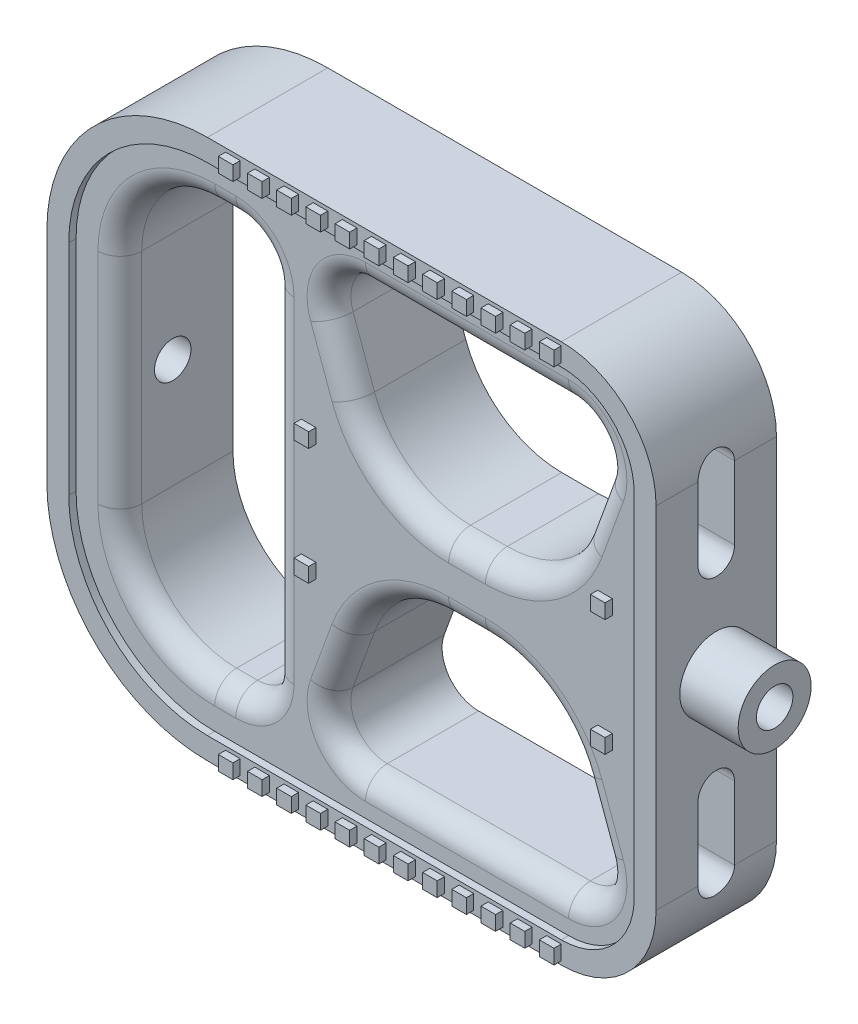
SolidWorks part; units mm, degrees
ref_plane "Front Plane" through (0, 0, 0) normal (0, 0, 1) x (1, 0, 0)
ref_plane "Top Plane" through (0, 0, 0) normal (0, 1, 0) x (1, 0, 0)
ref_plane "Right Plane" through (0, 0, 0) normal (1, 0, 0) x (0, 0, -1)
sketch "Sketch1" plane through (0, 0, 0) normal (0, 0, 1) x (1, 0, 0)
  line L1 (-41.75, 37) -> (41.75, 37)
  line L2 (-41.75, 37) -> (-41.75, -37)
  line L3 (-41.75, -37) -> (41.75, -37)
  line L4 (41.75, 37) -> (41.75, -37)
  line L5 (-41.75, 37) -> (41.75, -37) construction
  line L6 (-41.75, -37) -> (41.75, 37) construction
  point P0 (0, 0)
  dimension "D1" = 74
  dimension "D2" = 83.5
extrude "Boss-Extrude1" add sketch "Sketch1" along normal blind 16.5
fillet "Fillet1" radius 13 2 edges at (41.75, -37, 8.25) (41.75, 37, 8.25)
fillet "Fillet2" radius 22 2 edges at (-41.75, -37, 8.25) (-41.75, 37, 8.25)
sketch "Sketch2" plane through (0, 0, 16.5) normal (0, 0, 1) x (1, 0, 0)
  line L0 (-38.75, 15) -> (-38.75, -15)
  line L1 (-19.75, -34) -> (28.75, -34)
  line L2 (38.75, -24) -> (38.75, 24)
  line L3 (28.75, 34) -> (-19.75, 34)
  line L4 (-41.75, 15) -> (-41.75, -15)
  line L5 (-19.75, -37) -> (28.75, -37)
  line L6 (41.75, -24) -> (41.75, 24)
  line L7 (28.75, 37) -> (-19.75, 37)
  line L8 (-41.75, 15) -> (-41.75, -15)
  line L9 (-19.75, -37) -> (28.75, -37)
  line L10 (41.75, -24) -> (41.75, 24)
  line L11 (28.75, 37) -> (-19.75, 37)
  arc A0 (-19.75, 34) -> (-38.75, 15) centre (-19.75, 15) ccw
  arc A1 (-38.75, -15) -> (-19.75, -34) centre (-19.75, -15) ccw
  arc A2 (28.75, -34) -> (38.75, -24) centre (28.75, -24) ccw
  arc A3 (38.75, 24) -> (28.75, 34) centre (28.75, 24) ccw
  arc A4 (-41.75, -15) -> (-19.75, -37) centre (-19.75, -15) ccw
  arc A5 (28.75, -37) -> (41.75, -24) centre (28.75, -24) ccw
  arc A6 (41.75, 24) -> (28.75, 37) centre (28.75, 24) ccw
  arc A7 (-19.75, 37) -> (-41.75, 15) centre (-19.75, 15) ccw
  arc A8 (-41.75, -15) -> (-19.75, -37) centre (-19.75, -15) ccw
  arc A9 (28.75, -37) -> (41.75, -24) centre (28.75, -24) ccw
  arc A10 (41.75, 24) -> (28.75, 37) centre (28.75, 24) ccw
  arc A11 (-19.75, 37) -> (-41.75, 15) centre (-19.75, 15) ccw
  dimension "D1" = 0
  dimension "D2" = 3
extrude "Cut-Extrude1" cut sketch "Sketch2" against normal blind 1 contours A0 L0 A1 L1 A2 L2 A3 L3
sketch "Sketch4" plane through (41.75, 0, 0) normal (1, 0, 0) x (0, 0, -1)
  line L0 (-16.5, 0) -> (0, 0) construction
  line L3 (-16.5, -24) -> (-16.5, 24) construction
  line L6 (-8.25, 24) -> (-8.25, -24) construction
  line L7 (0, 24) -> (-16.5, 24) construction
  line L8 (-16.5, -24) -> (0, -24) construction
  circle A4 centre (-8.25, 0) radius 5
  dimension "D1" = 10
extrude "Boss-Extrude2" add sketch "Sketch4" along normal blind 8
sketch "Sketch5" plane through (41.75, 0, 0) normal (1, 0, 0) x (0, 0, -1)
  line L0 (-8.25, 24) -> (-8.25, 14) construction
  line L1 (-5.75, 24) -> (-5.75, 14)
  line L2 (-10.75, 24) -> (-10.75, 14)
  line L3 (-16.5, 0) -> (0, 0) construction
  line L4 (-16.5, -24) -> (-16.5, 24) construction
  line L5 (-8.25, -24) -> (-8.25, -14) construction
  line L6 (-5.75, -24) -> (-5.75, -14)
  line L7 (-10.75, -24) -> (-10.75, -14)
  line L8 (-16.5, -24) -> (-16.5, -37) construction
  line L9 (-16.5, -37) -> (0, -37) construction
  line L10 (0, -37) -> (0, -24) construction
  line L11 (0, -24) -> (-16.5, -24) construction
  line L12 (-16.5, 37) -> (-16.5, 24) construction
  line L13 (-16.5, 24) -> (0, 24) construction
  line L14 (0, 24) -> (0, 37) construction
  line L15 (0, 37) -> (-16.5, 37) construction
  line L16 (-16.5, -24) -> (-16.5, -37)
  line L17 (-16.5, -37) -> (0, -37)
  line L18 (0, -37) -> (0, -24)
  line L19 (0, -24) -> (-16.5, -24)
  line L20 (-16.5, 37) -> (-16.5, 24)
  line L21 (-16.5, 24) -> (0, 24)
  line L22 (0, 24) -> (0, 37)
  line L23 (0, 37) -> (-16.5, 37)
  circle A0 centre (-8.25, 0) radius 5 construction
  circle A1 centre (-8.25, 0) radius 5
  arc A2 (-5.75, 24) -> (-10.75, 24) centre (-8.25, 24) ccw
  arc A3 (-10.75, 14) -> (-5.75, 14) centre (-8.25, 14) ccw
  arc A4 (-5.75, -24) -> (-10.75, -24) centre (-8.25, -24) cw
  arc A5 (-10.75, -14) -> (-5.75, -14) centre (-8.25, -14) cw
  point P5 (-8.25, 19)
  point P17 (-8.25, -19)
  line M9 (-16.5, -24) -> (0, -24)
  line M11 (0, 24) -> (-16.5, 24)
  dimension "D1" = 10
  dimension "D2" = 5
  dimension "D3" = 14
sketch "Sketch6" plane through (0, 0, 15.5) normal (0, 0, 1) x (1, 0, 0)
  line L0 (-38.75, 0) -> (38.75, 0) construction
  line L1 (-19.75, 28) -> (-16.875, 28)
  line L2 (-32.75, 15) -> (-32.75, -15)
  line L3 (-19.75, -28) -> (-16.875, -28)
  line L4 (28.75, 34) -> (-19.75, 34)
  line L5 (-38.75, 15) -> (-38.75, -15)
  line L6 (-19.75, -34) -> (28.75, -34)
  line L7 (38.75, -24) -> (38.75, 24)
  line L8 (28.75, 34) -> (-19.75, 34)
  line L9 (-38.75, 15) -> (-38.75, -15)
  line L10 (-19.75, -34) -> (28.75, -34)
  line L11 (38.75, -24) -> (38.75, 24)
  line L12 (-11.875, 23) -> (-11.875, -23)
  line L13 (0.9167, 29) -> (28.75, 29)
  line L18 (33.4485, 22.2899) -> (30.5082, 14.2117)
  line L19 (17.3525, 5) -> (12.3141, 5)
  line L20 (-0.8416, 14.2117) -> (-3.7818, 22.2899)
  line L21 (17.3525, -5) -> (12.3141, -5)
  line L22 (33.4485, -22.2899) -> (30.5082, -14.2117)
  line L23 (0.9167, -29) -> (28.75, -29)
  line L24 (-0.8416, -14.2117) -> (-3.7818, -22.2899)
  arc A0 (-32.75, -15) -> (-19.75, -28) centre (-19.75, -15) ccw
  arc A1 (-19.75, 28) -> (-32.75, 15) centre (-19.75, 15) ccw
  arc A2 (-16.875, -28) -> (-11.875, -23) centre (-16.875, -23) ccw
  arc A3 (-16.875, 28) -> (-11.875, 23) centre (-16.875, 23) cw
  arc A4 (-19.75, 34) -> (-38.75, 15) centre (-19.75, 15) ccw
  arc A5 (-38.75, -15) -> (-19.75, -34) centre (-19.75, -15) ccw
  arc A6 (28.75, -34) -> (38.75, -24) centre (28.75, -24) ccw
  arc A7 (38.75, 24) -> (28.75, 34) centre (28.75, 24) ccw
  arc A8 (-19.75, 34) -> (-38.75, 15) centre (-19.75, 15) ccw
  arc A9 (-38.75, -15) -> (-19.75, -34) centre (-19.75, -15) ccw
  arc A10 (28.75, -34) -> (38.75, -24) centre (28.75, -24) ccw
  arc A11 (38.75, 24) -> (28.75, 34) centre (28.75, 24) ccw
  arc A12 (28.75, 29) -> (33.4485, 22.2899) centre (28.75, 24) cw
  arc A13 (0.9167, 29) -> (-3.7818, 22.2899) centre (0.9167, 24) ccw
  arc A14 (28.75, -29) -> (33.4485, -22.2899) centre (28.75, -24) ccw
  arc A15 (0.9167, -29) -> (-3.7818, -22.2899) centre (0.9167, -24) cw
  arc A16 (30.5082, 14.2117) -> (17.3525, 5) centre (17.3525, 19) cw
  arc A17 (12.3141, 5) -> (-0.8416, 14.2117) centre (12.3141, 19) cw
  arc A18 (17.3525, -5) -> (30.5082, -14.2117) centre (17.3525, -19) cw
  arc A19 (12.3141, -5) -> (-0.8416, -14.2117) centre (12.3141, -19) ccw
  point P18 (-32.75, -28)
  point P23 (-11.875, -28)
  point P46 (27.1555, 5)
  point P49 (2.5112, 5)
  point P52 (27.1555, -5)
  point P55 (2.5112, -5)
  dimension "D4" = 5
  dimension "D3" = 13
  dimension "D6" = 5
  dimension "D9" = 14
  dimension "D10" = 14
  dimension "D2" = 20.875
  dimension "D5" = 70
  dimension "D7" = 27.8333
  dimension "D8" = 10
  dimension "D1" = 0
extrude "Cut-Extrude2" cut sketch "Sketch6" against normal through all contours A1 L1 A3 L12 A2 L3 A0 L2 | L20 A13 L13 A12 L18 A16 L19 A17 | L21 A19 L24 A15 L23 A14 L22 A18
extrude "Cut-Extrude7" cut sketch "Sketch5" against normal up to next contours L2 A3 L1 M11 | L1 A2 L2 M11 | A5 L7 L6 M9 | A4 L6 L7 M9
sketch "Sketch7" plane through (49.75, 0, 0) normal (1, 0, 0) x (0, 0, -1)
  circle A0 centre (-8.25, 0) radius 2.5
  circle A1 centre (-8.25, 0) radius 5
  circle A2 centre (-8.25, 0) radius 5
  dimension "D2" = 5
  dimension "D1" = 0
extrude "Cut-Extrude9" cut sketch "Sketch7" against normal through all contours A0
fillet "Fillet3" radius 3 24 edges at (25.3826, -7.5319, 15.5) (31.9784, -18.2508, 15.5) (32.8458, -26.8679, 15.5) (14.8333, -29, 15.5) (-3.1791, -26.8679, 15.5) (-2.3117, -18.2508, 15.5) (4.284, -7.5319, 15.5) (25.3826, 7.5319, 15.5) (31.9784, 18.2508, 15.5) (32.8458, 26.8679, 15.5) (14.8333, 29, 15.5) (-3.1791, 26.8679, 15.5) (-2.3117, 18.2508, 15.5) (4.284, 7.5319, 15.5) (-28.9424, 24.1924, 15.5) (-18.3125, 28, 15.5) (-13.3395, 26.5355, 15.5) (-11.875, 0, 15.5) (-13.3395, -26.5355, 15.5) (-18.3125, -28, 15.5) (-28.9424, -24.1924, 15.5) (14.8333, -5, 15.5) (14.8333, 5, 15.5) (-32.75, 0, 15.5)
fillet "Fillet4" [suppressed] radius 1
sketch "Sketch8" plane through (0, 0, 15.5) normal (0, 0, 1) x (1, 0, 0)
  line L0 (-11.875, -23) -> (-11.875, 23) construction
  line L1 (-7.875, -7) -> (-5.875, -7)
  line L2 (-7.875, -7) -> (-7.875, -9)
  line L3 (-7.875, -9) -> (-5.875, -9)
  line L4 (-5.875, -7) -> (-5.875, -9)
  line L5 (32.75, -7) -> (34.75, -7)
  line L6 (32.75, -7) -> (32.75, -9)
  line L7 (32.75, -9) -> (34.75, -9)
  line L8 (34.75, -7) -> (34.75, -9)
  line L9 (41.75, -24) -> (41.75, 24) construction
  line L10 (-41.75, 0) -> (49.75, 0) construction
  line L11 (-41.75, 15) -> (-41.75, -15) construction
  line L12 (49.75, -5) -> (49.75, 5) construction
  line L13 (32.75, 9) -> (34.75, 9)
  line L14 (34.75, 7) -> (34.75, 9)
  line L15 (32.75, 7) -> (34.75, 7)
  line L16 (32.75, 7) -> (32.75, 9)
  line L17 (-7.875, 9) -> (-5.875, 9)
  line L18 (-5.875, 7) -> (-5.875, 9)
  line L19 (-7.875, 7) -> (-5.875, 7)
  line L20 (-7.875, 7) -> (-7.875, 9)
  line L22 (26.75, 36.5) -> (28.75, 36.5)
  line L23 (26.75, 36.5) -> (26.75, 34.5)
  line L24 (26.75, 34.5) -> (28.75, 34.5)
  line L25 (28.75, 36.5) -> (28.75, 34.5)
  line L26 (28.75, 37) -> (-19.75, 37) construction
  line L27 (22.75, 36.5) -> (22.75, 34.5)
  line L28 (22.75, 36.5) -> (24.75, 36.5)
  line L29 (24.75, 36.5) -> (24.75, 34.5)
  line L30 (22.75, 34.5) -> (24.75, 34.5)
  line L31 (18.75, 36.5) -> (18.75, 34.5)
  line L32 (18.75, 36.5) -> (20.75, 36.5)
  line L33 (20.75, 36.5) -> (20.75, 34.5)
  line L34 (18.75, 34.5) -> (20.75, 34.5)
  line L35 (14.75, 36.5) -> (14.75, 34.5)
  line L36 (14.75, 36.5) -> (16.75, 36.5)
  line L37 (16.75, 36.5) -> (16.75, 34.5)
  line L38 (14.75, 34.5) -> (16.75, 34.5)
  line L39 (10.75, 36.5) -> (10.75, 34.5)
  line L40 (10.75, 36.5) -> (12.75, 36.5)
  line L41 (12.75, 36.5) -> (12.75, 34.5)
  line L42 (10.75, 34.5) -> (12.75, 34.5)
  line L43 (6.75, 36.5) -> (6.75, 34.5)
  line L44 (6.75, 36.5) -> (8.75, 36.5)
  line L45 (8.75, 36.5) -> (8.75, 34.5)
  line L46 (6.75, 34.5) -> (8.75, 34.5)
  line L47 (2.75, 36.5) -> (2.75, 34.5)
  line L48 (2.75, 36.5) -> (4.75, 36.5)
  line L49 (4.75, 36.5) -> (4.75, 34.5)
  line L50 (2.75, 34.5) -> (4.75, 34.5)
  line L51 (-1.25, 36.5) -> (-1.25, 34.5)
  line L52 (-1.25, 36.5) -> (0.75, 36.5)
  line L53 (0.75, 36.5) -> (0.75, 34.5)
  line L54 (-1.25, 34.5) -> (0.75, 34.5)
  line L55 (-5.25, 36.5) -> (-5.25, 34.5)
  line L56 (-5.25, 36.5) -> (-3.25, 36.5)
  line L57 (-3.25, 36.5) -> (-3.25, 34.5)
  line L58 (-5.25, 34.5) -> (-3.25, 34.5)
  line L59 (-9.25, 36.5) -> (-9.25, 34.5)
  line L60 (-9.25, 36.5) -> (-7.25, 36.5)
  line L61 (-7.25, 36.5) -> (-7.25, 34.5)
  line L62 (-9.25, 34.5) -> (-7.25, 34.5)
  line L63 (-13.25, 36.5) -> (-13.25, 34.5)
  line L64 (-13.25, 36.5) -> (-11.25, 36.5)
  line L65 (-11.25, 36.5) -> (-11.25, 34.5)
  line L66 (-13.25, 34.5) -> (-11.25, 34.5)
  line L67 (-17.25, 36.5) -> (-17.25, 34.5)
  line L68 (-17.25, 36.5) -> (-15.25, 36.5)
  line L69 (-15.25, 36.5) -> (-15.25, 34.5)
  line L70 (-17.25, 34.5) -> (-15.25, 34.5)
  line L71 (28.75, -36.5) -> (28.75, -34.5)
  line L72 (26.75, -36.5) -> (28.75, -36.5)
  line L73 (26.75, -36.5) -> (26.75, -34.5)
  line L74 (26.75, -34.5) -> (28.75, -34.5)
  line L75 (24.75, -36.5) -> (24.75, -34.5)
  line L76 (22.75, -34.5) -> (24.75, -34.5)
  line L77 (22.75, -36.5) -> (22.75, -34.5)
  line L78 (22.75, -36.5) -> (24.75, -36.5)
  line L79 (20.75, -36.5) -> (20.75, -34.5)
  line L80 (18.75, -34.5) -> (20.75, -34.5)
  line L81 (18.75, -36.5) -> (18.75, -34.5)
  line L82 (18.75, -36.5) -> (20.75, -36.5)
  line L83 (16.75, -36.5) -> (16.75, -34.5)
  line L84 (14.75, -34.5) -> (16.75, -34.5)
  line L85 (14.75, -36.5) -> (14.75, -34.5)
  line L86 (14.75, -36.5) -> (16.75, -36.5)
  line L87 (12.75, -36.5) -> (12.75, -34.5)
  line L88 (10.75, -34.5) -> (12.75, -34.5)
  line L89 (10.75, -36.5) -> (10.75, -34.5)
  line L90 (10.75, -36.5) -> (12.75, -36.5)
  line L91 (8.75, -36.5) -> (8.75, -34.5)
  line L92 (6.75, -34.5) -> (8.75, -34.5)
  line L93 (6.75, -36.5) -> (6.75, -34.5)
  line L94 (6.75, -36.5) -> (8.75, -36.5)
  line L95 (4.75, -36.5) -> (4.75, -34.5)
  line L96 (2.75, -34.5) -> (4.75, -34.5)
  line L97 (2.75, -36.5) -> (2.75, -34.5)
  line L98 (2.75, -36.5) -> (4.75, -36.5)
  line L99 (0.75, -36.5) -> (0.75, -34.5)
  line L100 (-1.25, -34.5) -> (0.75, -34.5)
  line L101 (-1.25, -36.5) -> (-1.25, -34.5)
  line L102 (-1.25, -36.5) -> (0.75, -36.5)
  line L103 (-3.25, -36.5) -> (-3.25, -34.5)
  line L104 (-5.25, -34.5) -> (-3.25, -34.5)
  line L105 (-5.25, -36.5) -> (-5.25, -34.5)
  line L106 (-5.25, -36.5) -> (-3.25, -36.5)
  line L107 (-7.25, -36.5) -> (-7.25, -34.5)
  line L108 (-9.25, -34.5) -> (-7.25, -34.5)
  line L109 (-9.25, -36.5) -> (-9.25, -34.5)
  line L110 (-9.25, -36.5) -> (-7.25, -36.5)
  line L111 (-11.25, -36.5) -> (-11.25, -34.5)
  line L112 (-13.25, -34.5) -> (-11.25, -34.5)
  line L113 (-13.25, -36.5) -> (-13.25, -34.5)
  line L114 (-13.25, -36.5) -> (-11.25, -36.5)
  line L115 (-15.25, -36.5) -> (-15.25, -34.5)
  line L116 (-17.25, -34.5) -> (-15.25, -34.5)
  line L117 (-17.25, -36.5) -> (-17.25, -34.5)
  line L118 (-17.25, -36.5) -> (-15.25, -36.5)
  dimension "D1" = 2
  dimension "D2" = 2
  dimension "D3" = 4
  dimension "D4" = 2
  dimension "D5" = 2
  dimension "D6" = 7
  dimension "D7" = 14
  dimension "D8" = 14
  dimension "D9" = 2
  dimension "D10" = 2
  dimension "D11" = 0.5
  dimension "D12" = 13
  dimension "D14" = 4
  dimension "D16" = 4
  dimension "D13" = 12
  dimension "D15" = 12
extrude "Boss-Extrude4" add sketch "Sketch8" along normal blind 1
sketch "Sketch9" plane through (0, 0, 16.5) normal (0, 0, 1) x (1, 0, 0)
  line L0 (28.75, 37) -> (-19.75, 37) construction
  line L1 (26.75, 36.5) -> (28.75, 36.5)
  line L2 (26.75, 36.5) -> (26.75, 34.5)
  line L3 (26.75, 34.5) -> (28.75, 34.5)
  line L4 (28.75, 36.5) -> (28.75, 34.5)
  line L5 (41.75, -24) -> (41.75, 24) construction
  line L6 (-41.75, 0) -> (49.75, 0) construction
  line L7 (-41.75, 15) -> (-41.75, -15) construction
  line L8 (49.75, -5) -> (49.75, 5) construction
  line L9 (26.75, -34.5) -> (28.75, -34.5)
  line L10 (28.75, -36.5) -> (28.75, -34.5)
  line L11 (26.75, -36.5) -> (28.75, -36.5)
  line L12 (26.75, -36.5) -> (26.75, -34.5)
  line L13 (22.75, 36.5) -> (22.75, 34.5)
  line L14 (22.75, 36.5) -> (24.75, 36.5)
  line L15 (24.75, 36.5) -> (24.75, 34.5)
  line L16 (22.75, 34.5) -> (24.75, 34.5)
  line L17 (22.75, -34.5) -> (24.75, -34.5)
  line L18 (24.75, -36.5) -> (24.75, -34.5)
  line L19 (22.75, -36.5) -> (24.75, -36.5)
  line L20 (22.75, -36.5) -> (22.75, -34.5)
  line L21 (18.75, 36.5) -> (18.75, 34.5)
  line L22 (18.75, 36.5) -> (20.75, 36.5)
  line L23 (20.75, 36.5) -> (20.75, 34.5)
  line L24 (18.75, 34.5) -> (20.75, 34.5)
  line L25 (18.75, -34.5) -> (20.75, -34.5)
  line L26 (20.75, -36.5) -> (20.75, -34.5)
  line L27 (18.75, -36.5) -> (20.75, -36.5)
  line L28 (18.75, -36.5) -> (18.75, -34.5)
  line L29 (14.75, 36.5) -> (14.75, 34.5)
  line L30 (14.75, 36.5) -> (16.75, 36.5)
  line L31 (16.75, 36.5) -> (16.75, 34.5)
  line L32 (14.75, 34.5) -> (16.75, 34.5)
  line L33 (14.75, -34.5) -> (16.75, -34.5)
  line L34 (16.75, -36.5) -> (16.75, -34.5)
  line L35 (14.75, -36.5) -> (16.75, -36.5)
  line L36 (14.75, -36.5) -> (14.75, -34.5)
  line L37 (10.75, 36.5) -> (10.75, 34.5)
  line L38 (10.75, 36.5) -> (12.75, 36.5)
  line L39 (12.75, 36.5) -> (12.75, 34.5)
  line L40 (10.75, 34.5) -> (12.75, 34.5)
  line L41 (10.75, -34.5) -> (12.75, -34.5)
  line L42 (12.75, -36.5) -> (12.75, -34.5)
  line L43 (10.75, -36.5) -> (12.75, -36.5)
  line L44 (10.75, -36.5) -> (10.75, -34.5)
  line L45 (6.75, 36.5) -> (6.75, 34.5)
  line L46 (6.75, 36.5) -> (8.75, 36.5)
  line L47 (8.75, 36.5) -> (8.75, 34.5)
  line L48 (6.75, 34.5) -> (8.75, 34.5)
  line L49 (6.75, -34.5) -> (8.75, -34.5)
  line L50 (8.75, -36.5) -> (8.75, -34.5)
  line L51 (6.75, -36.5) -> (8.75, -36.5)
  line L52 (6.75, -36.5) -> (6.75, -34.5)
  line L53 (2.75, 36.5) -> (2.75, 34.5)
  line L54 (2.75, 36.5) -> (4.75, 36.5)
  line L55 (4.75, 36.5) -> (4.75, 34.5)
  line L56 (2.75, 34.5) -> (4.75, 34.5)
  line L57 (2.75, -34.5) -> (4.75, -34.5)
  line L58 (4.75, -36.5) -> (4.75, -34.5)
  line L59 (2.75, -36.5) -> (4.75, -36.5)
  line L60 (2.75, -36.5) -> (2.75, -34.5)
  line L61 (-1.25, 36.5) -> (-1.25, 34.5)
  line L62 (-1.25, 36.5) -> (0.75, 36.5)
  line L63 (0.75, 36.5) -> (0.75, 34.5)
  line L64 (-1.25, 34.5) -> (0.75, 34.5)
  line L65 (-1.25, -34.5) -> (0.75, -34.5)
  line L66 (0.75, -36.5) -> (0.75, -34.5)
  line L67 (-1.25, -36.5) -> (0.75, -36.5)
  line L68 (-1.25, -36.5) -> (-1.25, -34.5)
  line L69 (-5.25, 36.5) -> (-5.25, 34.5)
  line L70 (-5.25, 36.5) -> (-3.25, 36.5)
  line L71 (-3.25, 36.5) -> (-3.25, 34.5)
  line L72 (-5.25, 34.5) -> (-3.25, 34.5)
  line L73 (-5.25, -34.5) -> (-3.25, -34.5)
  line L74 (-3.25, -36.5) -> (-3.25, -34.5)
  line L75 (-5.25, -36.5) -> (-3.25, -36.5)
  line L76 (-5.25, -36.5) -> (-5.25, -34.5)
  line L77 (-9.25, 36.5) -> (-9.25, 34.5)
  line L78 (-9.25, 36.5) -> (-7.25, 36.5)
  line L79 (-7.25, 36.5) -> (-7.25, 34.5)
  line L80 (-9.25, 34.5) -> (-7.25, 34.5)
  line L81 (-9.25, -34.5) -> (-7.25, -34.5)
  line L82 (-7.25, -36.5) -> (-7.25, -34.5)
  line L83 (-9.25, -36.5) -> (-7.25, -36.5)
  line L84 (-9.25, -36.5) -> (-9.25, -34.5)
  line L85 (-13.25, 36.5) -> (-13.25, 34.5)
  line L86 (-13.25, 36.5) -> (-11.25, 36.5)
  line L87 (-11.25, 36.5) -> (-11.25, 34.5)
  line L88 (-13.25, 34.5) -> (-11.25, 34.5)
  line L89 (-13.25, -34.5) -> (-11.25, -34.5)
  line L90 (-11.25, -36.5) -> (-11.25, -34.5)
  line L91 (-13.25, -36.5) -> (-11.25, -36.5)
  line L92 (-13.25, -36.5) -> (-13.25, -34.5)
  line L93 (-17.25, 36.5) -> (-17.25, 34.5)
  line L94 (-17.25, 36.5) -> (-15.25, 36.5)
  line L95 (-15.25, 36.5) -> (-15.25, 34.5)
  line L96 (-17.25, 34.5) -> (-15.25, 34.5)
  line L97 (-17.25, -34.5) -> (-15.25, -34.5)
  line L98 (-15.25, -36.5) -> (-15.25, -34.5)
  line L99 (-17.25, -36.5) -> (-15.25, -36.5)
  line L100 (-17.25, -36.5) -> (-17.25, -34.5)
  dimension "D1" = 2
  dimension "D2" = 2
  dimension "D3" = 0.5
  dimension "D4" = 13
  dimension "D6" = 4
  dimension "D5" = 12
extrude "Boss-Extrude5" add sketch "Sketch9" along normal blind 1
equation "\"A\"= 74"
equation "\"B\"= 83.5"
equation "\"C\"= 16.5"
equation "\"D1@Sketch1\"= \"A\""
equation "\"D2@Sketch1\"= \"B\""
equation "\"D1@Boss-Extrude1\"=\"C\""
equation "\"D2@Sketch6\"=\"B\"/4"
equation "\"D7@Sketch6\"=\"B\"/3"
